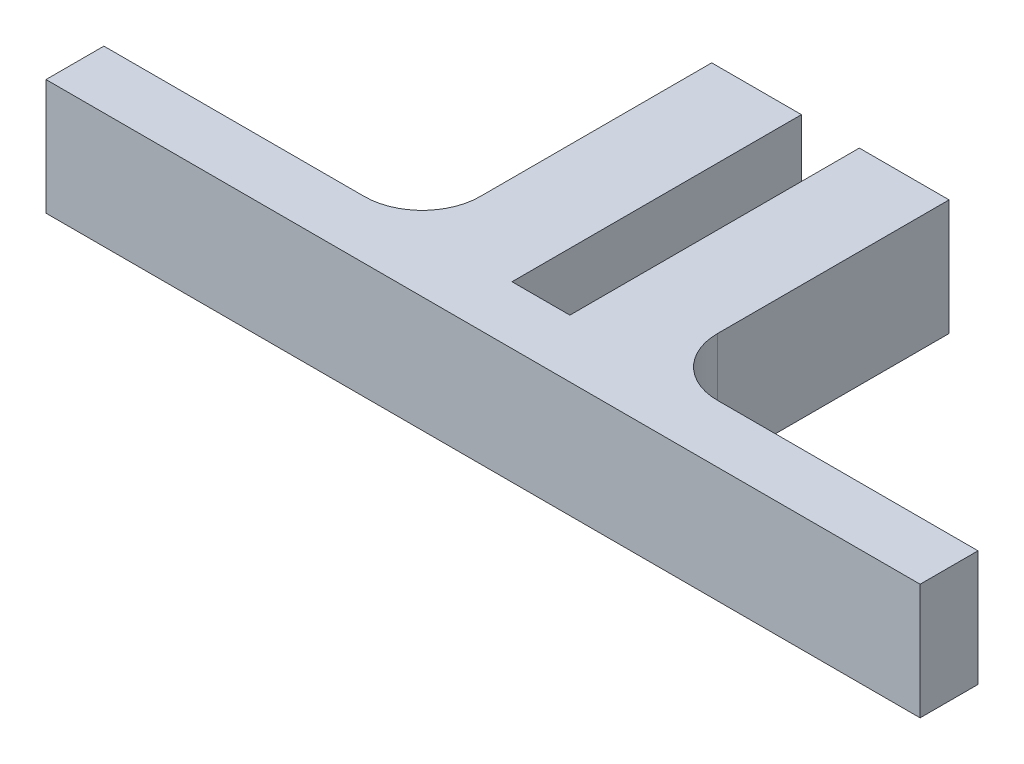
SolidWorks part; units mm, degrees
ref_plane "Front Plane" through (0, 0, 0) normal (0, 0, 1) x (1, 0, 0)
ref_plane "Top Plane" through (0, 0, 0) normal (0, 1, 0) x (1, 0, 0)
ref_plane "Right Plane" through (0, 0, 0) normal (1, 0, 0) x (0, 0, -1)
sketch "Sketch1" plane through (0, 0, 0) normal (0, 1, 0) x (1, 0, 0)
  line L0 (-80.6967, 52.0203) -> (-35.6967, 52.0203)
  line L1 (25.3033, 52.0203) -> (70.3033, 52.0203)
  line L2 (-80.6967, 52.0203) -> (-80.6967, 42.0203)
  line L3 (-80.6967, 42.0203) -> (70.3033, 42.0203)
  line L4 (70.3033, 52.0203) -> (70.3033, 42.0203)
  line L9 (15.3033, 102.0203) -> (-25.6967, 102.0203)
  line L10 (15.3033, 102.0203) -> (15.3033, 62.0203)
  line L12 (-25.6967, 102.0203) -> (-25.6967, 62.0203)
  arc A0 (25.3033, 52.0203) -> (15.3033, 62.0203) centre (25.3033, 62.0203) cw
  arc A1 (-35.6967, 52.0203) -> (-25.6967, 62.0203) centre (-35.6967, 62.0203) ccw
  point P12 (-25.6967, 52.0203)
  dimension "D1" = 10
  dimension "D4" = 10
  dimension "D2" = 55
  dimension "D3" = 10
  dimension "D5" = 41
  dimension "D6" = 55
extrude "Boss-Extrude2" add sketch "Sketch1" along normal blind 20
sketch "Sketch4" plane through (0, 0, -102.0203) normal (0, 0, -1) x (-1, 0, 0)
  line L0 (-15.3033, 20) -> (25.6967, 20) construction
  line L1 (10.1967, 0) -> (0.1967, 0)
  line L2 (10.1967, 0) -> (10.1967, 20)
  line L3 (10.1967, 20) -> (0.1967, 20)
  line L4 (0.1967, 0) -> (0.1967, 20)
  line L5 (-15.3033, 0) -> (25.6967, 0) construction
  line L6 (25.6967, 20) -> (25.6967, 0) construction
  dimension "D1" = 10
  dimension "D2" = 0
  dimension "D3" = 0
  dimension "D4" = 15.5
extrude "Cut-Extrude1" cut sketch "Sketch4" against normal blind 50 contours L2 L1 L4 L3
